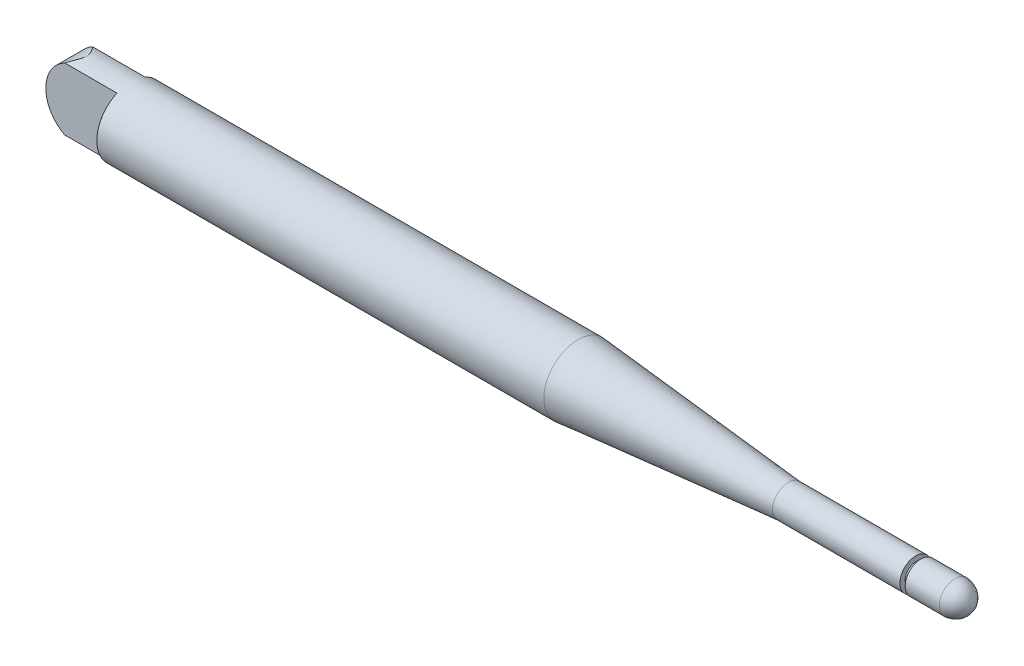
SolidWorks part; units mm, degrees
material "ABS"
ref_plane "Płaszczyzna XY" through (0, 0, 0) normal (0, 0, 1) x (1, 0, 0)
ref_plane "Płaszczyzna XZ" through (0, 0, 0) normal (0, 1, 0) x (1, 0, 0)
ref_plane "Płaszczyzna YZ" through (0, 0, 0) normal (1, 0, 0) x (0, 0, -1)
sketch "Sketch1" plane through (0, 0, 0) normal (0, 0, 1) x (1, 0, 0)
  line L0 (0, 0) -> (0, -6.5)
  line L1 (0, -6.5) -> (85, -6.5)
  line L2 (85, -6.5) -> (125, -3)
  line L3 (125, -3) -> (149.222, -3)
  line L4 (149.222, -3) -> (149.222, -2)
  line L5 (149.222, -2) -> (150.222, -2)
  line L6 (150.222, -2) -> (150.222, -3)
  line L7 (150.222, -3) -> (156.707, -3)
  line L8 (0, 0) -> (160, 0)
  arc A0 (156.707, -3) -> (160, 0) centre (156.707, 0.3073) ccw
  dimension "D9" = 3.3073
  dimension "D1" = 6.5
  dimension "D2" = 3
  dimension "D3" = 160
  dimension "D4" = 1
  dimension "D5" = 1
  dimension "D6" = 85
  dimension "D7" = 125
  dimension "D8" = 10.778
revolve "Revolve1" add sketch "Sketch1" angle 360 about L8
sketch "Sketch2" plane through (0, 0, 0) normal (-1, 0, 0) x (0, 0, 1)
  line L0 (-2.6588, 5.9313) -> (-2.6588, -5.9313)
  line L1 (2.6588, 5.9313) -> (2.6588, -5.9313)
  arc A0 (-2.6588, -5.9313) -> (2.6588, -5.9313) centre (0, 0) ccw
  circle A1 centre (0, 0) radius 6.5
  arc A2 (2.6588, 5.9313) -> (-2.6588, 5.9313) centre (0, 0) ccw
  dimension "D2" = 11.8627
  dimension "D3" = 11.8627
  dimension "D1" = 0
extrude "Boss-Extrude1" add sketch "Sketch2" along normal blind 13.5
sketch "Sketch3" plane through (0, 0, 2.6588) normal (0, 0, 1) x (1, 0, 0)
  line L2 (-7.2711, 6.6693) -> (-14.2425, 7.6196)
  line L3 (-14.2425, 7.6196) -> (-14.8128, -7.6566)
  line L4 (-14.8128, -7.6566) -> (-6.2474, -8.5291)
  line L5 (-6.2474, -8.5291) -> (-7.6329, -6.6595)
  line L8 (0, -5.9313) -> (0, 5.9313) construction
  line L9 (-13.5, 5.9313) -> (0, 5.9313) construction
  arc A0 (-7.2711, 6.6693) -> (-7.6329, -6.6595) centre (-6.8431, -0.0116) ccw
  dimension "D1" = 6.6946
  dimension "D2" = 6.2474
  dimension "D3" = 6.8431
  dimension "D4" = 7.2711
  dimension "D5" = 7.6329
  dimension "D6" = 14.2425
  dimension "D7" = 14.8128
  dimension "D8" = 0.7379
  dimension "D9" = 1.6883
  dimension "D12" = 13.588
  dimension "D13" = 14.4605
extrude "Cut-Extrude1" cut sketch "Sketch3" against normal blind 13.5
sketch "Sketch4" plane through (0, 0, 2.6588) normal (0, 0, 1) x (1, 0, 0)
  line L4 (-13.5, 0.6975) -> (-13.5, -0.7208)
  line L5 (-9.9695, -5.9313) -> (0, -5.9313)
  line L6 (0, -5.9313) -> (0, 5.9313)
  line L7 (0, 5.9313) -> (-9.9251, 5.9313)
  line L8 (-13.5, 0.6975) -> (-13.5, -0.7208)
  line L9 (-9.9695, -5.9313) -> (0, -5.9313)
  line L10 (0, -5.9313) -> (0, 5.9313)
  line L11 (0, 5.9313) -> (-9.9251, 5.9313)
  arc A2 (-13.5, -0.7208) -> (-9.9695, -5.9313) centre (-6.8431, -0.0116) ccw
  arc A3 (-9.9251, 5.9313) -> (-13.5, 0.6975) centre (-6.8431, -0.0116) ccw
  arc A4 (-13.5, -0.7208) -> (-9.9695, -5.9313) centre (-6.8431, -0.0116) ccw
  arc A5 (-9.9251, 5.9313) -> (-13.5, 0.6975) centre (-6.8431, -0.0116) ccw
  dimension "D1" = 0
